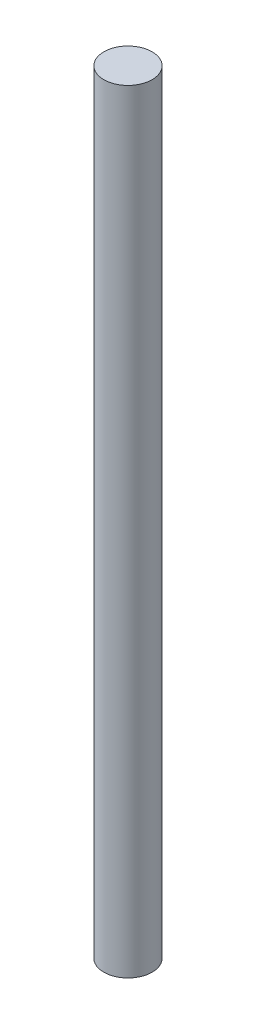
SolidWorks part; units mm, degrees
ref_plane "Front Plane" through (0, 0, 0) normal (0, 0, 1) x (1, 0, 0)
ref_plane "Top Plane" through (0, 0, 0) normal (0, 1, 0) x (1, 0, 0)
ref_plane "Right Plane" through (0, 0, 0) normal (1, 0, 0) x (0, 0, -1)
sketch "Sketch1" plane through (0, 0, 0) normal (0, 1, 0) x (1, 0, 0)
  circle A0 centre (0, 0) radius 6.35
  dimension "D1" = 12.7
extrude "Boss-Extrude1" add sketch "Sketch1" along normal blind 203.2
